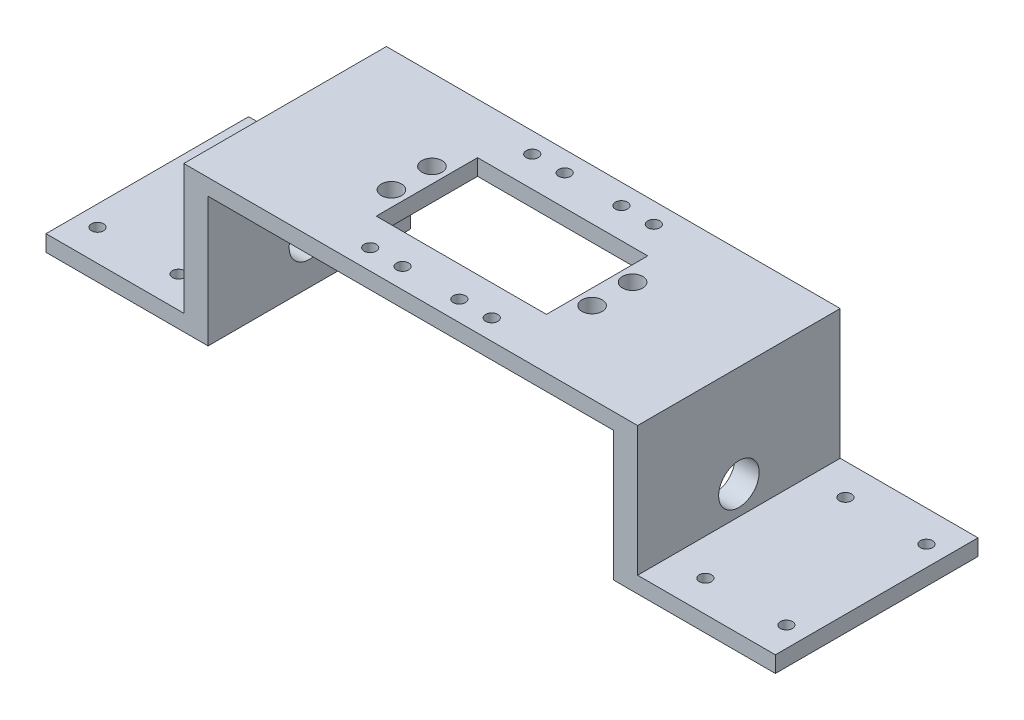
SolidWorks part; units mm, degrees
ref_plane "前视基准面" through (0, 0, 0) normal (0, 0, 1) x (1, 0, 0)
ref_plane "上视基准面" through (0, 0, 0) normal (0, 1, 0) x (1, 0, 0)
ref_plane "右视基准面" through (0, 0, 0) normal (1, 0, 0) x (0, 0, -1)
sketch "草图1" plane through (0, 0, 0) normal (0, 0, 1) x (1, 0, 0)
  line L0 (-58.9635, 0) -> (63.0177, 0) construction
  line L1 (0, 44.0901) -> (0, -22.3211) construction
  line L2 (90, 0) -> (90, 4)
  line L3 (90, 4) -> (56, 4)
  line L4 (56, 4) -> (56, 36)
  line L5 (56, 36) -> (-56, 36)
  line L7 (-50, 32) -> (50, 32)
  line L8 (50, 32) -> (50, 0)
  line L9 (50, 0) -> (90, 0)
  line L10 (-50, 0) -> (-90, 0)
  line L11 (-50, 32) -> (-50, 0)
  line L12 (-90, 0) -> (-90, 4)
  line L13 (-90, 4) -> (-56, 4)
  line L14 (-56, 4) -> (-56, 36)
  point P9 (-90, 2)
  dimension "D1" = 32
  dimension "D2" = 100
  dimension "D3" = 6
  dimension "D4" = 4
  dimension "D5" = 4
  dimension "D6" = 180
extrude "凸台-拉伸1" add sketch "草图1" against normal blind 50
sketch "草图2" plane through (0, 36, 0) normal (0, 1, 0) x (1, 0, 0)
  line L0 (-56, 25) -> (56, 25) construction
  line L1 (-56, 50) -> (-56, 0) construction
  line L2 (56, 50) -> (56, 0) construction
  line L3 (0, 50) -> (0, 0) construction
  line L4 (56, 50) -> (-56, 50) construction
  line L6 (-21, 37.5) -> (21, 37.5)
  line L7 (-21, 37.5) -> (-21, 12.5)
  line L8 (-21, 12.5) -> (21, 12.5)
  line L9 (21, 37.5) -> (21, 12.5)
  line L10 (-21, 37.5) -> (21, 12.5) construction
  line L11 (-21, 12.5) -> (21, 37.5) construction
  point P11 (0, 25)
  dimension "D1" = 25
  dimension "D2" = 42
extrude "切除-拉伸1" cut sketch "草图2" against normal through all
sketch "草图3" plane through (0, 36, 0) normal (0, 1, 0) x (1, 0, 0)
  line L0 (-56, 25) -> (56, 25) construction
  line L1 (-56, 50) -> (-56, 0) construction
  line L2 (56, 50) -> (56, 0) construction
  line L3 (0, 50) -> (0, 0) construction
  line L4 (56, 50) -> (-56, 50) construction
  line L5 (56, 0) -> (-56, 0) construction
  circle A0 centre (-24.76, 30) radius 2.5
  circle A1 centre (24.76, 30) radius 2.5
  circle A2 centre (24.76, 20) radius 2.5
  circle A3 centre (-24.76, 20) radius 2.5
  dimension "D1" = 5
  dimension "D2" = 24.76
  dimension "D3" = 5
extrude "切除-拉伸2" cut sketch "草图3" against normal through all
sketch "草图4" plane through (56, 0, 0) normal (1, 0, 0) x (0, 0, -1)
  line L0 (25, 36) -> (25, 4) construction
  line L1 (50, 36) -> (0, 36) construction
  line L2 (50, 4) -> (0, 4) construction
  circle A0 centre (25, 11) radius 5
  dimension "D1" = 10
  dimension "D2" = 7
extrude "切除-拉伸3" cut sketch "草图4" against normal through all
sketch "草图5" plane through (0, 4, 0) normal (0, 1, 0) x (1, 0, 0)
  line L0 (-90, 25) -> (90, 25) construction
  line L1 (-90, 50) -> (-90, 0) construction
  line L2 (90, 50) -> (90, 0) construction
  line L3 (56, 50) -> (-56, 50) construction
  line L4 (0, 50) -> (0, 25) construction
  line L5 (0, 25) -> (0, 0) construction
  circle A0 centre (-36.608, 54.7496) radius 1.5
  circle A5 centre (-65, 42.286) radius 1.5
  circle A6 centre (-65, 7.714) radius 1.5
  circle A7 centre (-36.608, -4.7496) radius 1.5
  circle A8 centre (36.608, -4.7496) radius 1.5
  circle A9 centre (65, 7.714) radius 1.5
  circle A10 centre (65, 42.286) radius 1.5
  circle A11 centre (36.608, 54.7496) radius 1.5
  circle A12 centre (85, 7.714) radius 1.5
  circle A13 centre (85, 42.286) radius 1.5
  circle A14 centre (-85, 42.286) radius 1.5
  circle A15 centre (-85, 7.714) radius 1.5
  dimension "D1" = 3
  dimension "D2" = 3
  dimension "D3" = 130
  dimension "D4" = 3
  dimension "D5" = 3
  dimension "D6" = 20
  dimension "D7" = 20
extrude "切除-拉伸4" cut sketch "草图5" against normal through all
sketch "草图6" plane through (0, 36, 0) normal (0, 1, 0) x (1, 0, 0)
  line L0 (-56, 45) -> (56, 45) construction
  line L1 (-56, 50) -> (-56, 0) construction
  line L2 (56, 50) -> (56, 0) construction
  line L3 (56, 50) -> (-56, 50) construction
  line L4 (-56, 25) -> (56, 25) construction
  line L5 (0, 50) -> (0, 37.5) construction
  line L6 (21, 37.5) -> (-21, 37.5) construction
  circle A0 centre (-7, 45) radius 1.5
  circle A1 centre (7, 45) radius 1.5
  circle A2 centre (-15, 45) radius 1.5
  circle A3 centre (15, 45) radius 1.5
  circle A4 centre (15, 5) radius 1.5
  circle A5 centre (7, 5) radius 1.5
  circle A6 centre (-7, 5) radius 1.5
  circle A7 centre (-15, 5) radius 1.5
  dimension "D2" = 3
  dimension "D4" = 3
  dimension "D1" = 5
  dimension "D3" = 14
  dimension "D5" = 8
extrude "切除-拉伸5" cut sketch "草图6" against normal through all
